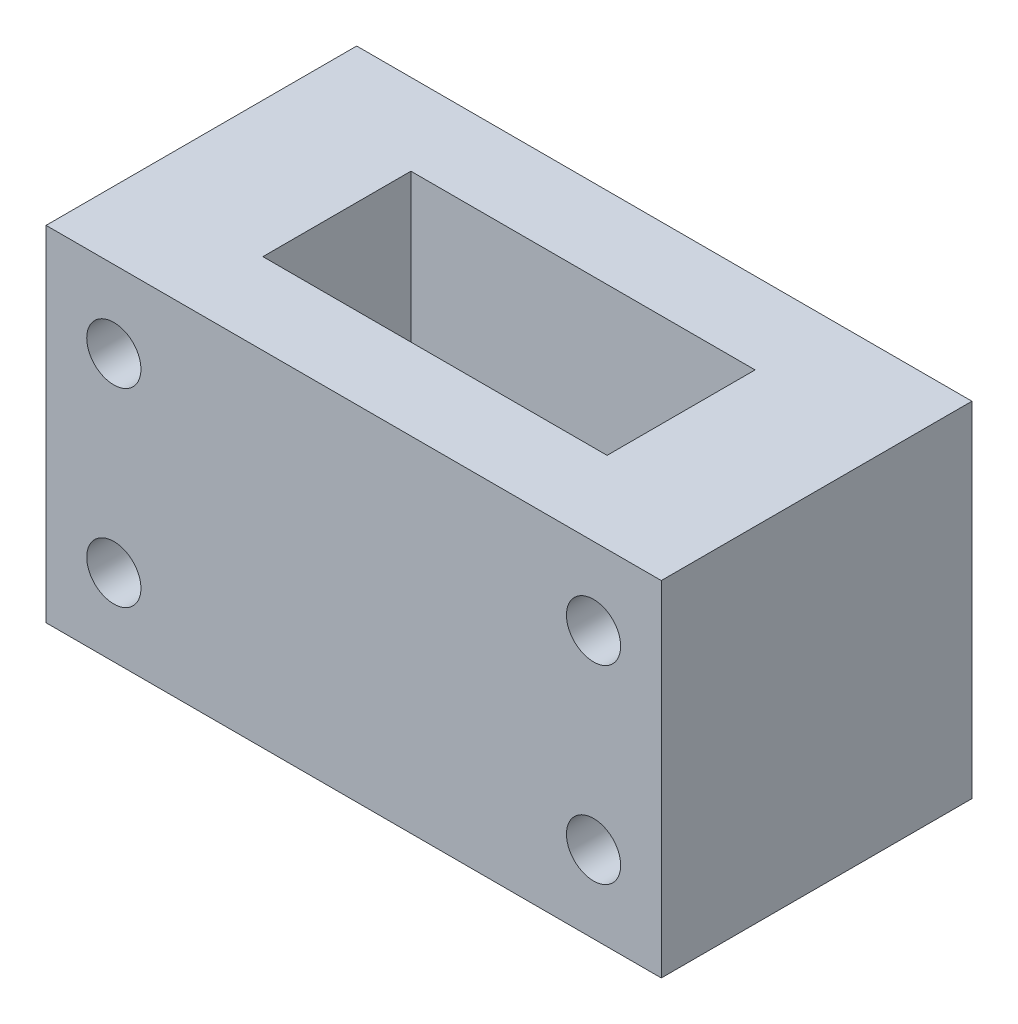
SolidWorks part; units mm, degrees
ref_plane "Front Plane" through (0, 0, 0) normal (0, 0, 1) x (1, 0, 0)
ref_plane "Top Plane" through (0, 0, 0) normal (0, 1, 0) x (1, 0, 0)
ref_plane "Right Plane" through (0, 0, 0) normal (1, 0, 0) x (0, 0, -1)
sketch "Sketch1" plane through (0, 0, 0) normal (0, 1, 0) x (1, 0, 0)
  line L1 (-22.7, 11.461) -> (22.7, 11.461)
  line L2 (-22.7, 11.461) -> (-22.7, -11.461)
  line L3 (-22.7, -11.461) -> (22.7, -11.461)
  line L4 (22.7, 11.461) -> (22.7, -11.461)
  line L5 (-22.7, 11.461) -> (22.7, -11.461) construction
  line L6 (-22.7, -11.461) -> (22.7, 11.461) construction
  line L7 (-12.7, -5.461) -> (12.7, -5.461)
  line L8 (-12.7, -5.461) -> (-12.7, 5.461)
  line L9 (-12.7, 5.461) -> (12.7, 5.461)
  line L10 (12.7, -5.461) -> (12.7, 5.461)
  line L11 (-12.7, -5.461) -> (12.7, 5.461) construction
  line L12 (-12.7, 5.461) -> (12.7, -5.461) construction
  point P0 (0, 0)
  point P7 (0, 0)
  dimension "D1" = 10
  dimension "D2" = 10.922
  dimension "D3" = 6
  dimension "D4" = 25.4
extrude "Boss-Extrude1" add sketch "Sketch1" along normal blind 25.4
sketch "Sketch2" plane through (0, 0, -11.461) normal (0, 0, -1) x (-1, 0, 0)
  line L0 (-22.7, 25.4) -> (-22.7, 0) construction
  line L1 (-22.7, 12.7) -> (22.7, 12.7) construction
  line L2 (22.7, 25.4) -> (22.7, 0) construction
  line L3 (0, 0) -> (0, 25.4) construction
  line L4 (-22.7, 25.4) -> (22.7, 25.4) construction
  circle A0 centre (-17.7, 5.7) radius 2
  circle A3 centre (-17.7, 19.7) radius 2
  circle A4 centre (17.7, 19.7) radius 2
  circle A5 centre (17.7, 5.7) radius 2
  dimension "D2" = 4
  dimension "D1" = 5
  dimension "D3" = 7
extrude "Cut-Extrude1" cut sketch "Sketch2" against normal through all
